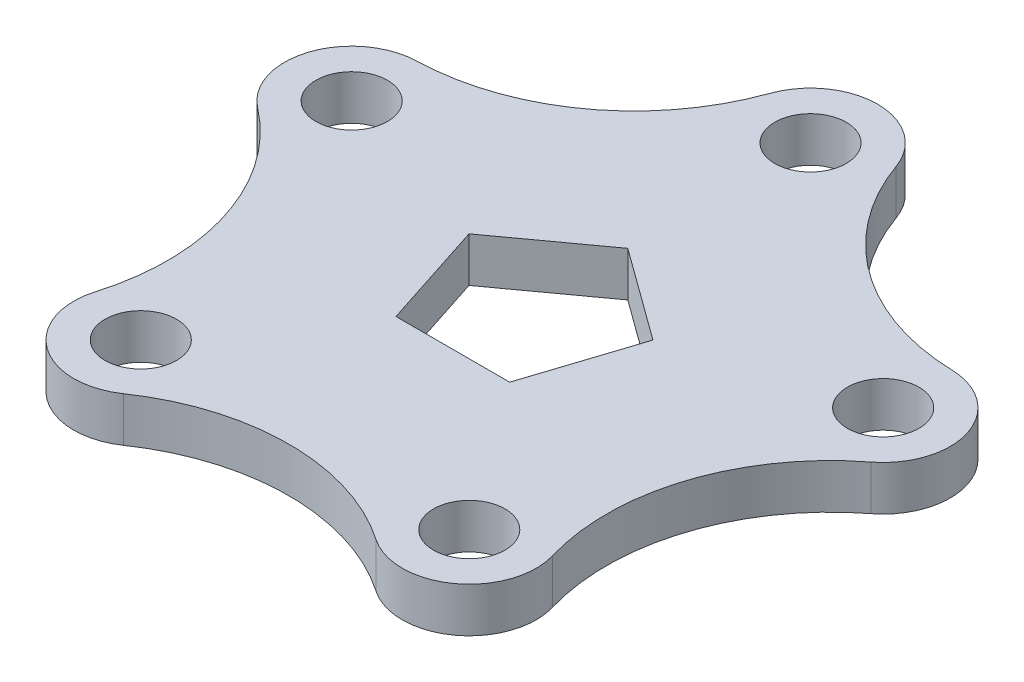
SolidWorks part; units mm, degrees
ref_plane "Front Plane" through (0, 0, 0) normal (0, 0, 1) x (1, 0, 0)
ref_plane "Top Plane" through (0, 0, 0) normal (0, 1, 0) x (1, 0, 0)
ref_plane "Right Plane" through (0, 0, 0) normal (1, 0, 0) x (0, 0, -1)
sketch "Sketch1" plane through (0, 0, 0) normal (0, 1, 0) x (1, 0, 0)
  line L1 (0, 21.6312) -> (-20.5725, 6.6844)
  line L2 (-20.5725, 6.6844) -> (-12.7145, -17.5)
  line L3 (-12.7145, -17.5) -> (12.7145, -17.5)
  line L4 (12.7145, -17.5) -> (20.5725, 6.6844)
  line L5 (20.5725, 6.6844) -> (0, 21.6312)
  arc A13 (14.1321, 67.5282) -> (-14.1321, 67.5282) centre (0, 62.5) ccw
  arc A14 (68.5902, 7.4269) -> (59.856, 34.3078) centre (59.441, 19.3136) ccw
  arc A15 (28.2589, -62.9381) -> (51.1252, -46.3248) centre (36.7366, -50.5636) ccw
  arc A16 (-51.1252, -46.3248) -> (-28.2589, -62.9381) centre (-36.7366, -50.5636) ccw
  arc A17 (-59.856, 34.3078) -> (-68.5902, 7.4269) centre (-59.441, 19.3136) ccw
  arc A18 (-59.856, 34.3078) -> (-14.1321, 67.5282) centre (-61.2393, 84.2887) ccw
  arc A22 (-68.5902, 7.4269) -> (-51.1252, -46.3248) centre (-99.0873, -32.1954) cw
  arc A23 (-28.2589, -62.9381) -> (28.2589, -62.9381) centre (0, -104.1865) cw
  arc A24 (51.1252, -46.3248) -> (68.5902, 7.4269) centre (99.0873, -32.1954) cw
  arc A25 (14.1321, 67.5282) -> (59.856, 34.3078) centre (61.2393, 84.2887) ccw
  circle A26 centre (0, 62.5) radius 8
  circle A27 centre (-59.441, 19.3136) radius 8
  circle A28 centre (59.441, 19.3136) radius 8
  circle A29 centre (-36.7366, -50.5636) radius 8
  circle A30 centre (36.7366, -50.5636) radius 8
  circle A31 centre (0, 0) radius 17.5
  circle A32 centre (0, 0) radius 17.5 construction
  point P14 (0, 0)
  point P16 (0, 0)
  point P26 (0, 0)
  dimension "D2" = 30
  dimension "D4" = 50
  dimension "D6" = 50
  dimension "D5" = 50
  dimension "D7" = 50
  dimension "D8" = 50
  dimension "D9" = 16
  dimension "D10" = 16
  dimension "D11" = 16
  dimension "D12" = 16
  dimension "D13" = 16
  dimension "D14" = 35
  dimension "D3" = 5
extrude "Boss-Extrude3" add sketch "Sketch1" along normal blind 10 contours A25 A13 A18 A17 A22 A16 A23 A15 A24 A14 A30 A29 A28 A27 A26 L5 L4 L3 L2 L1
